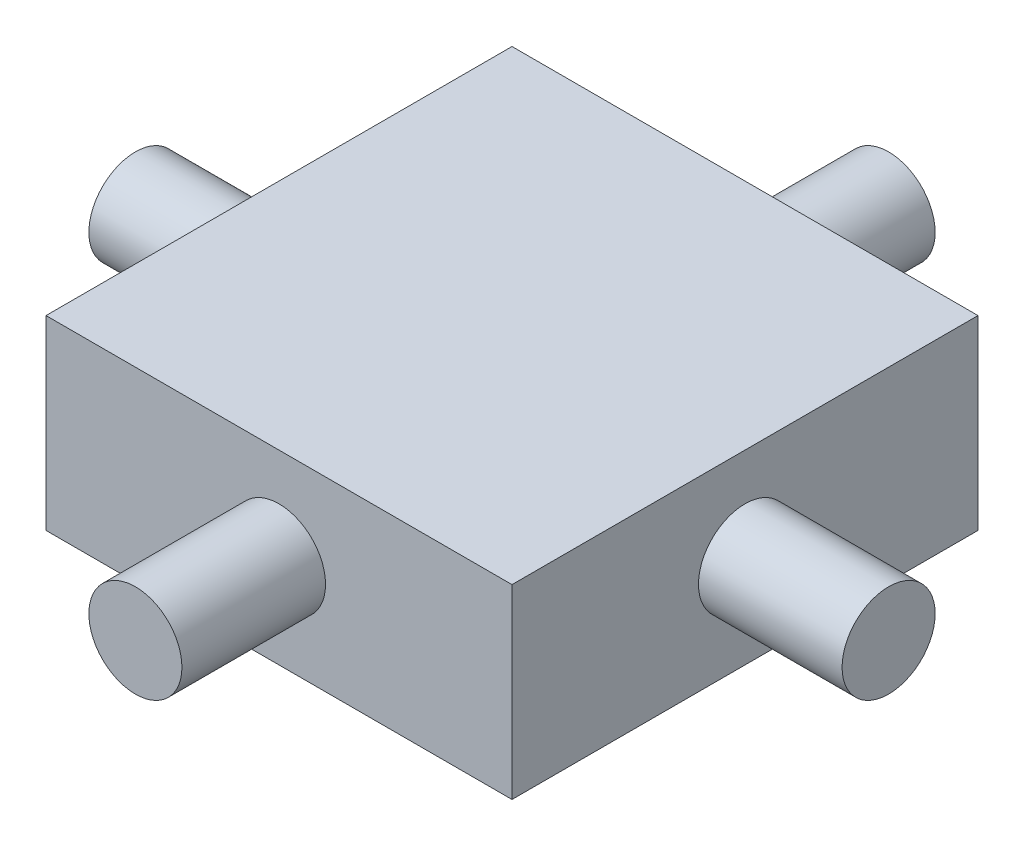
SolidWorks part; units mm, degrees
material "1060 Alloy"
ref_plane "Front Plane" through (0, 0, 0) normal (0, 0, 1) x (1, 0, 0)
ref_plane "Top Plane" through (0, 0, 0) normal (0, 1, 0) x (1, 0, 0)
ref_plane "Right Plane" through (0, 0, 0) normal (1, 0, 0) x (0, 0, -1)
sketch "Sketch5" plane through (0, 0, 0) normal (0, 0, 1) x (1, 0, 0)
  line L0 (-60.7432, -4.5214) -> (-60.7432, -17.2214)
  line L1 (-60.7432, -17.2214) -> (-28.9432, -17.2214)
  line L2 (-28.9432, -17.2214) -> (-28.9432, -4.5214)
  line L3 (-60.7432, -4.5214) -> (-28.9432, -4.5214)
extrude "Boss-Extrude4" add sketch "Sketch5" along normal blind 31.8
sketch "Sketch6" plane through (0, 0, 31.8) normal (0, 0, 1) x (1, 0, 0)
  line L0 (-60.7432, -4.5214) -> (-28.9432, -17.2214) construction
  line L1 (-28.9432, -17.2214) -> (-28.9432, -4.5214) construction
  line L2 (-28.9432, -4.5214) -> (-60.7432, -17.2214) construction
  circle A0 centre (-44.8432, -10.8714) radius 3.175
  point P4 (-44.8432, -10.8714)
  dimension "D1" = 6.35
extrude "Boss-Extrude5" add sketch "Sketch6" along normal blind 9.8
ref_plane "Plane1" through (0, 0, 15.9) normal (0, 0, 1) x (1, 0, 0)
mirror "Mirror1" about plane through (0, 0, 15.9) normal (0, 0, 1) of "Boss-Extrude5"
ref_plane "Plane2" through (-44.8432, 0, 0) normal (1, 0, 0) x (0, 0, -1)
sketch "Sketch10" plane through (-28.9432, 0, 0) normal (1, 0, 0) x (0, 0, -1)
  line L0 (-31.8, -17.2214) -> (0, -4.5214) construction
  line L1 (0, -4.5214) -> (0, -17.2214) construction
  line L2 (0, -17.2214) -> (-31.8, -4.5214) construction
  circle A0 centre (-15.9, -10.8714) radius 3.175
extrude "Boss-Extrude6" add sketch "Sketch10" along normal blind 9.8 contours A0
mirror "Mirror2" about plane through (-44.8432, 0, 0) normal (1, 0, 0) of "Boss-Extrude6"
sketch "Sketch11" plane through (0, 0, 15.9) normal (0, 0, 1) x (1, 0, 0)
  line L0 (-28.9432, -17.2214) -> (-60.7432, -4.5214) construction
  line L1 (-60.7432, -4.5214) -> (-60.7432, -17.2214) construction
  line L2 (-60.7432, -17.2214) -> (-28.9432, -4.5214) construction
  point P8 (-44.8432, -10.8714)
